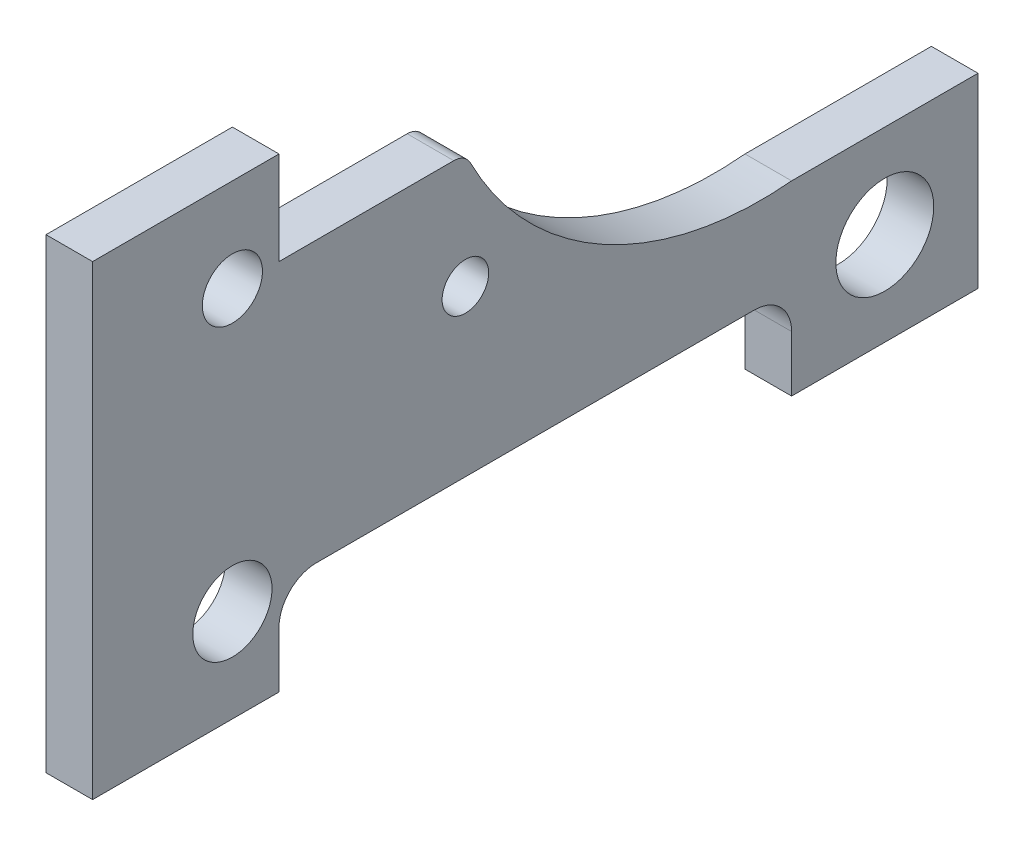
SolidWorks part; units mm, degrees
ref_plane "Front Plane" through (0, 0, 0) normal (0, 0, 1) x (1, 0, 0)
ref_plane "Top Plane" through (0, 0, 0) normal (0, 1, 0) x (1, 0, 0)
ref_plane "Right Plane" through (0, 0, 0) normal (1, 0, 0) x (0, 0, -1)
sketch "Sketch7" plane through (0, 0, 0) normal (1, 0, 0) x (0, 0, -1)
  line L0 (0, 0) -> (20, 0)
  line L1 (20, 0) -> (20, 10)
  line L2 (20, 10) -> (75, 10)
  line L3 (75, 10) -> (75, 0)
  line L4 (75, 0) -> (95, 0)
  line L5 (95, 0) -> (95, 20)
  line L6 (95, 20) -> (75, 20)
  line L7 (0, 0) -> (0, 50)
  line L8 (0, 50) -> (20, 50)
  line L9 (20, 50) -> (20, 40)
  line L10 (20, 40) -> (40, 40)
  arc A0 (40, 40) -> (75, 20) centre (71.6964, 54.8437) ccw
  circle A1 centre (15, 40) radius 3.225
  circle A2 centre (15, 10) radius 4.25
  circle A3 centre (40, 27.7001) radius 2.5
  circle A4 centre (85, 10) radius 5.25
  point P22 (0, 0)
  point P23 (0, 0)
  dimension "D11" = 35
  dimension "D12" = 6.45
  dimension "D14" = 5
  dimension "D15" = 10.5
  dimension "D17" = 8.5
  dimension "D1" = 20
  dimension "D2" = 10
  dimension "D3" = 95
  dimension "D4" = 55
  dimension "D5" = 20
  dimension "D6" = 50
  dimension "D7" = 20
  dimension "D8" = 10
  dimension "D9" = 40
  dimension "D10" = 20
  dimension "D13" = 30
  dimension "D16" = 25
extrude "Boss-Extrude5" add sketch "Sketch7" along normal blind 5
fillet "Fillet1" radius 4 2 edges at (2.5, 10, -75) (2.5, 10, -20)
fillet "Fillet2" radius 2 1 edges at (2.5, 40, -40)
